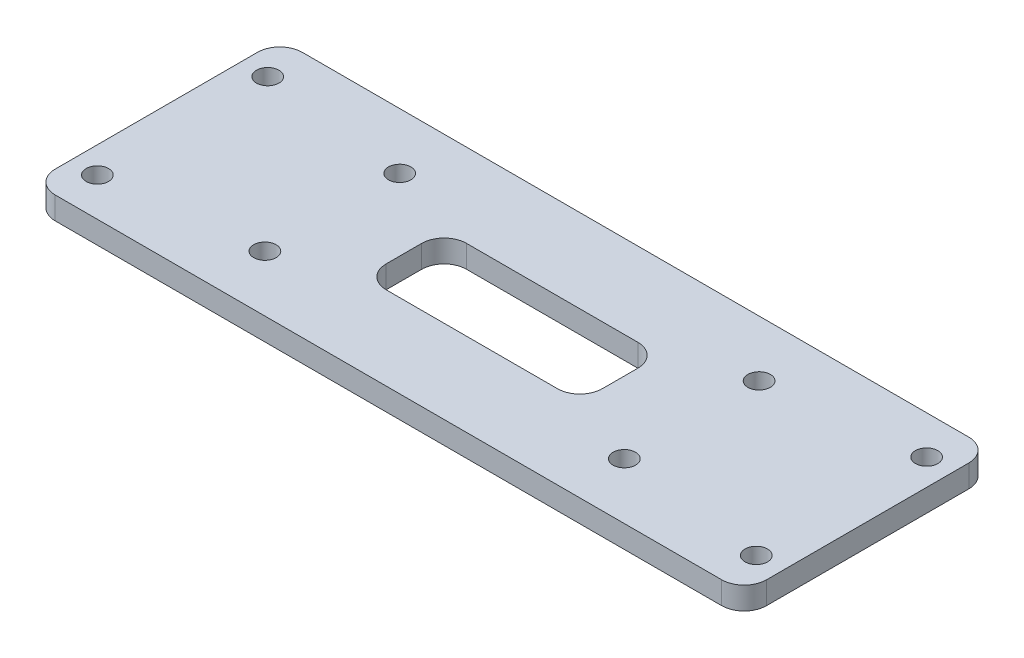
SolidWorks part; units mm, degrees
ref_plane "前视基准面" through (0, 0, 0) normal (0, 0, 1) x (1, 0, 0)
ref_plane "上视基准面" through (0, 0, 0) normal (0, 1, 0) x (1, 0, 0)
ref_plane "右视基准面" through (0, 0, 0) normal (1, 0, 0) x (0, 0, -1)
sketch "草图1" plane through (0, 0, 0) normal (0, 1, 0) x (1, 0, 0)
  line L1 (47.5, -16.5) -> (-47.5, -16.5)
  line L2 (47.5, -16.5) -> (47.5, 16.5)
  line L3 (47.5, 16.5) -> (-47.5, 16.5)
  line L4 (-47.5, -16.5) -> (-47.5, 16.5)
  line L5 (47.5, -16.5) -> (-47.5, 16.5) construction
  line L6 (47.5, 16.5) -> (-47.5, -16.5) construction
  point P0 (0, 0)
extrude "凸台-拉伸1" add sketch "草图1" along normal blind 3
sketch "草图2" plane through (0, 3, 0) normal (0, 1, 0) x (1, 0, 0)
  line L1 (44, 11.375) -> (-44, 11.375) construction
  line L2 (44, 11.375) -> (44, -11.375) construction
  line L3 (44, -11.375) -> (-44, -11.375) construction
  line L4 (-44, 11.375) -> (-44, -11.375) construction
  line L5 (44, 11.375) -> (-44, -11.375) construction
  line L6 (44, -11.375) -> (-44, 11.375) construction
  circle A0 centre (-44, 11.375) radius 1.5
  circle A1 centre (-44, -11.375) radius 1.5
  circle A2 centre (44, -11.375) radius 1.5
  circle A3 centre (44, 11.375) radius 1.5
  point P0 (0, 0)
extrude "切除-拉伸1" cut sketch "草图2" against normal through all
sketch "草图3" plane through (0, 3, 0) normal (0, 1, 0) x (1, 0, 0)
  line L1 (24, -9) -> (-24, -9) construction
  line L2 (24, -9) -> (24, 9) construction
  line L3 (24, 9) -> (-24, 9) construction
  line L4 (-24, -9) -> (-24, 9) construction
  line L5 (24, -9) -> (-24, 9) construction
  line L6 (24, 9) -> (-24, -9) construction
  circle A0 centre (-24, 9) radius 1.5
  circle A1 centre (24, 9) radius 1.5
  circle A2 centre (-24, -9) radius 1.5
  circle A3 centre (24, -9) radius 1.5
  point P0 (0, 0)
extrude "切除-拉伸2" cut sketch "草图3" against normal through all
fillet "圆角1" radius 3 4 edges at (47.5, 1.5, -16.5) (47.5, 1.5, 16.5) (-47.5, 1.5, 16.5) (-47.5, 1.5, -16.5)
sketch "草图4" plane through (0, 3, 0) normal (0, 1, 0) x (1, 0, 0)
  line L1 (14.4362, -5.3693) -> (-14.4362, -5.3693)
  line L2 (14.4362, -5.3693) -> (14.4362, 5.3693)
  line L3 (14.4362, 5.3693) -> (-14.4362, 5.3693)
  line L4 (-14.4362, -5.3693) -> (-14.4362, 5.3693)
  line L5 (14.4362, -5.3693) -> (-14.4362, 5.3693) construction
  line L6 (14.4362, 5.3693) -> (-14.4362, -5.3693) construction
  point P0 (0, 0)
extrude "切除-拉伸3" cut sketch "草图4" against normal through all
fillet "圆角2" radius 3 4 edges at (14.4362, 1.5, 5.3693) (14.4362, 1.5, -5.3693) (-14.4362, 1.5, 5.3693) (-14.4362, 1.5, -5.3693)
